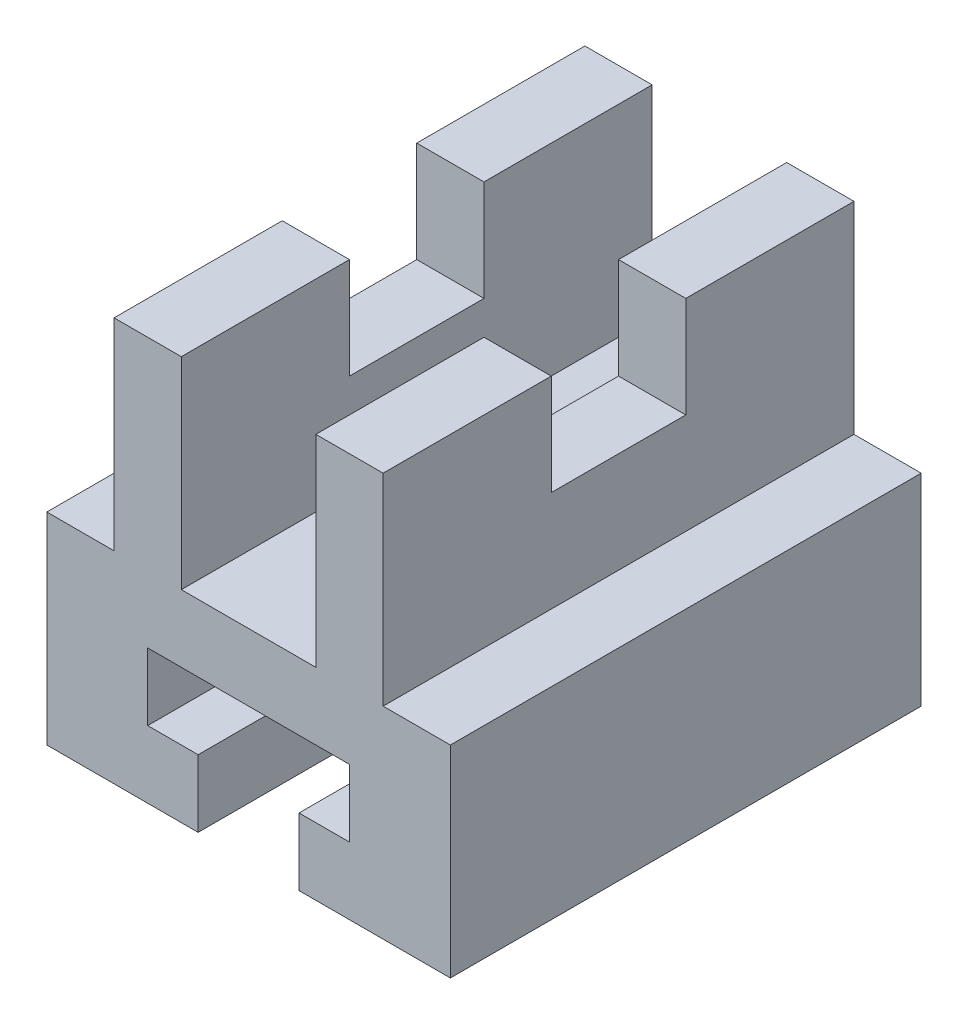
SolidWorks part; units mm, degrees
ref_plane "Ön Düzlem" through (0, 0, 0) normal (0, 0, 1) x (1, 0, 0)
ref_plane "Üst Düzlem" through (0, 0, 0) normal (0, 1, 0) x (1, 0, 0)
ref_plane "Sağ Düzlem" through (0, 0, 0) normal (1, 0, 0) x (0, 0, -1)
sketch "Çizim1" plane through (0, 0, 0) normal (0, 0, 1) x (1, 0, 0)
  line L1 (-35.6354, 25.3073) -> (24.3646, 25.3073)
  line L2 (-35.6354, 25.3073) -> (-35.6354, -34.6927)
  line L3 (-35.6354, -34.6927) -> (24.3646, -34.6927)
  line L4 (24.3646, 25.3073) -> (24.3646, -34.6927)
  dimension "D1" = 60
  dimension "D2" = 60
extrude "Yükseklik-Ekstrüzyon1" add sketch "Çizim1" along normal blind 70
sketch "Çizim2" plane through (0, 0, 70) normal (0, 0, 1) x (1, 0, 0)
  line L0 (9.3646, -24.6927) -> (1.8646, -24.6927)
  line L1 (-35.6354, -34.6927) -> (24.3646, -34.6927) construction
  line L2 (-5.6354, -34.6927) -> (-13.1354, -34.6927)
  line L3 (-13.1354, -34.6927) -> (-13.1354, -24.6927)
  line L4 (-13.1354, -24.6927) -> (-20.6354, -24.6927)
  line L5 (-20.6354, -24.6927) -> (-20.6354, -14.6927)
  line L6 (-20.6354, -14.6927) -> (9.3646, -14.6927)
  line L7 (9.3646, -14.6927) -> (9.3646, -24.6927)
  line L8 (1.8646, -24.6927) -> (1.8646, -34.6927)
  line L9 (1.8646, -34.6927) -> (-5.6354, -34.6927)
extrude "Kes-Ekstrüzyon1" cut sketch "Çizim2" against normal blind 70
sketch "Çizim3" plane through (0, 0, 70) normal (0, 0, 1) x (1, 0, 0)
  line L0 (24.3646, -4.6927) -> (14.3646, -4.6927)
  line L1 (14.3646, -4.6927) -> (14.3646, 25.3073)
  line L2 (24.3646, 25.3073) -> (-35.6354, 25.3073) construction
  line L3 (14.3646, 25.3073) -> (24.3646, 25.3073)
  line L4 (24.3646, 25.3073) -> (24.3646, -4.6927)
  line L5 (-35.6354, -4.6927) -> (-25.6354, -4.6927)
  line L6 (-25.6354, -4.6927) -> (-25.6354, 25.3073)
  line L7 (-25.6354, 25.3073) -> (-35.6354, 25.3073)
  line L8 (-35.6354, 25.3073) -> (-35.6354, -4.6927)
extrude "Kes-Ekstrüzyon2" cut sketch "Çizim3" against normal blind 70
sketch "Çizim4" plane through (0, 0, 70) normal (0, 0, 1) x (1, 0, 0)
  line L2 (14.3646, 25.3073) -> (-25.6354, 25.3073) construction
  line L3 (-15.6354, 25.3073) -> (-15.6354, -4.6927)
  line L4 (-15.6354, -4.6927) -> (4.3646, -4.6927)
  line L5 (4.3646, -4.6927) -> (4.3646, 25.3073)
  line L6 (4.3646, 25.3073) -> (-15.6354, 25.3073)
  dimension "D2" = 30
  dimension "D3" = 20
extrude "Kes-Ekstrüzyon5" cut sketch "Çizim4" against normal blind 70
sketch "Çizim5" plane through (-25.6354, 0, 0) normal (-1, 0, 0) x (0, 0, 1)
  line L1 (0, 25.3073) -> (70, 25.3073) construction
  line L2 (25, 25.3073) -> (25, 10.3073)
  line L3 (25, 10.3073) -> (45, 10.3073)
  line L4 (45, 10.3073) -> (45, 25.3073)
  line L5 (45, 25.3073) -> (25, 25.3073)
  dimension "D2" = 15
  dimension "D3" = 20
extrude "Kes-Ekstrüzyon6" cut sketch "Çizim5" against normal blind 40
